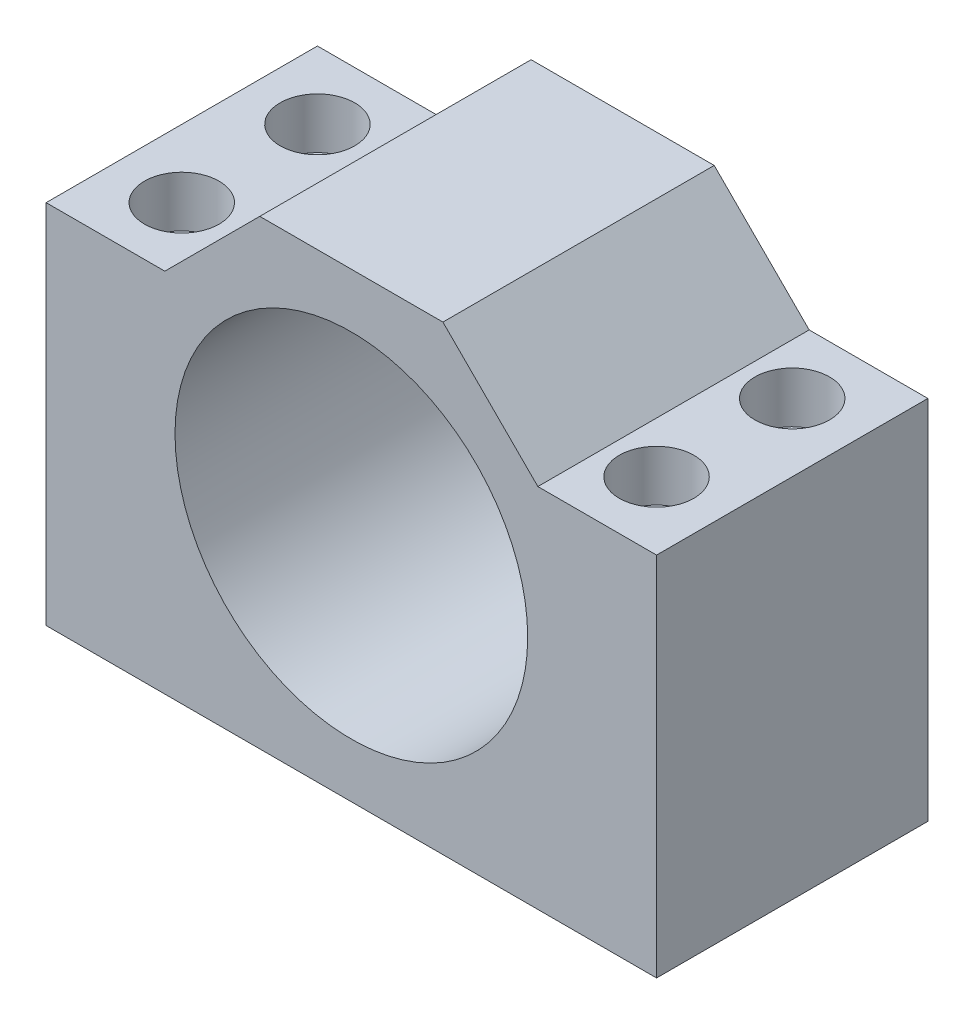
SolidWorks part; units mm, degrees
ref_plane "Front Plane" through (0, 0, 0) normal (0, 0, 1) x (1, 0, 0)
ref_plane "Top Plane" through (0, 0, 0) normal (0, 1, 0) x (1, 0, 0)
ref_plane "Right Plane" through (0, 0, 0) normal (1, 0, 0) x (0, 0, -1)
ref_plane "Plane1"
sketch "Sketch1" plane through (0, 0, 0) normal (0, 0, 1) x (1, 0, 0)
  line L0 (3.8657, -44.0908) -> (93.8657, -44.0908)
  line L1 (93.8657, -44.0908) -> (93.8657, 9.9092)
  line L2 (93.8657, 9.9092) -> (76.3657, 9.9092)
  line L3 (76.3657, 9.9092) -> (62.3657, 23.9092)
  line L4 (62.3657, 23.9092) -> (35.3657, 23.9092)
  line L5 (35.3657, 23.9092) -> (21.3657, 9.9092)
  line L6 (21.3657, 9.9092) -> (3.8657, 9.9092)
  line L7 (3.8657, 9.9092) -> (3.8657, -44.0908)
  circle A0 centre (48.8657, -10.0908) radius 26
  dimension "D7" = 52
  dimension "D1" = 90
  dimension "D2" = 54
  dimension "D3" = 55
  dimension "D4" = 27
  dimension "D5" = 17.5
  dimension "D6" = 19.799
  dimension "D8" = 34
  dimension "D9" = 34
  dimension "D10" = 45
extrude "Extrusion1" add sketch "Sketch1" along normal blind 40 contours L6 L7 L0 L1 L2 L3 L4 L5 A0
hole_wizard "Hole1" positions "Sketch3" profile "Sketch2" counterbore size "M6" standard "ANSI Metric" end condition through all
sketch "Sketch3" plane through (0, 9.9092, 0) normal (0, 1, 0) x (1, 0, 0)
  point P1 (13.8657, -10)
  point P2 (13.8657, -30)
  point P3 (83.8657, -10)
  point P4 (83.8657, -30)
sketch "Sketch2" plane through (13.8657, 9.9092, 10) normal (1, 0, 0) x (0, 0, 1)
  line L0 (0, 0) -> (0, 54)
  line L1 (0, 54) -> (3.3, 54)
  line L3 (3.3, 54) -> (3.3, 7.5)
  line L4 (3.3, 7.5) -> (5.5, 7.5)
  line L5 (5.5, 7.5) -> (5.5, 0)
  line L7 (5.5, 0) -> (0, 0)
  line L11 (0, -6.35) -> (0, 107.95) construction
  dimension "Thru Hole Dia." = 6.6
  dimension "Thru Hole Depth" = 54
  dimension "C'Bore Dia." = 11
  dimension "C'Bore Depth" = 7.5
